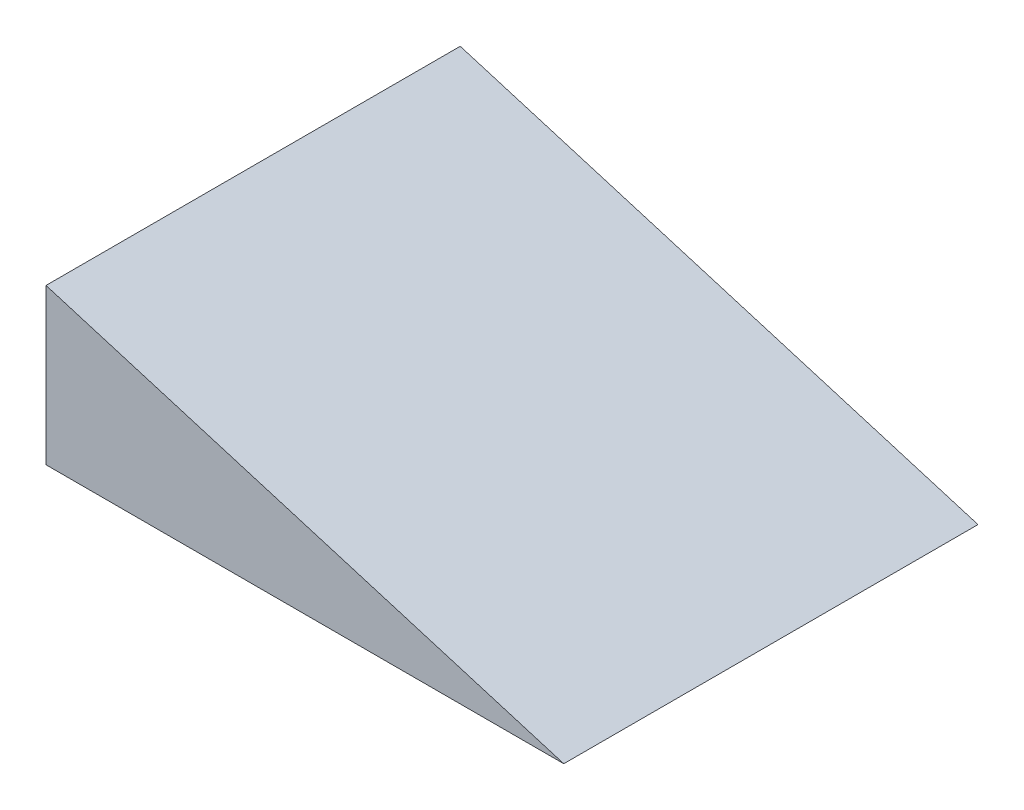
SolidWorks part; units mm, degrees
material "Balsa"
ref_plane "Front Plane" through (0, 0, 0) normal (0, 0, 1) x (1, 0, 0)
ref_plane "Top Plane" through (0, 0, 0) normal (0, 1, 0) x (1, 0, 0)
ref_plane "Right Plane" through (0, 0, 0) normal (1, 0, 0) x (0, 0, -1)
sketch "Sketch1" plane through (0, 0, 0) normal (0, 0, 1) x (1, 0, 0)
  line L0 (0, 228.6) -> (0, 0)
  line L1 (0, 0) -> (762, 0)
  line L2 (762, 0) -> (0, 228.6)
  dimension "D1" = 762
  dimension "D2" = 228.6
extrude "Boss-Extrude1" add sketch "Sketch1" against normal blind 609.6
shell "Shell1" thickness 6.35
sketch "Sketch2" plane through (62.9174, 209.7248, 0) normal (0.2873, 0.9578, 0) x (0.9578, -0.2873, 0)
  line L1 (-65.6877, 609.6) -> (729.8636, 609.6)
  line L2 (-65.6877, 609.6) -> (-65.6877, 0)
  line L3 (-65.6877, 0) -> (729.8636, 0)
  line L4 (729.8636, 609.6) -> (729.8636, 0)
